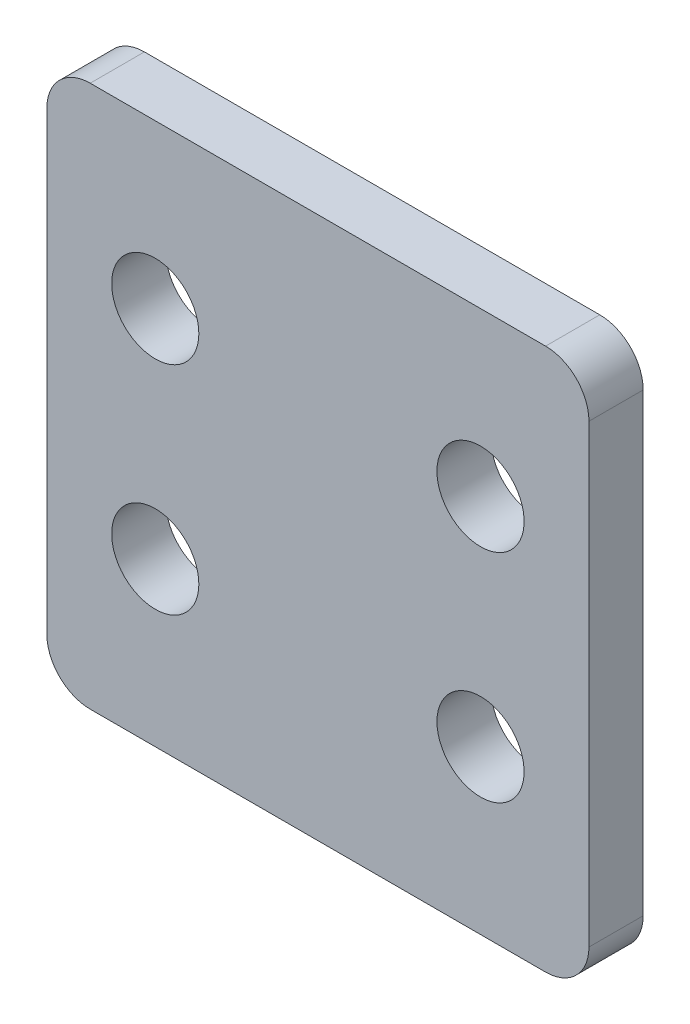
SolidWorks part; units mm, degrees
material "6061-T6 (SS)"
ref_plane "Front Plane" through (0, 0, 0) normal (0, 0, 1) x (1, 0, 0)
ref_plane "Top Plane" through (0, 0, 0) normal (0, 1, 0) x (1, 0, 0)
ref_plane "Right Plane" through (0, 0, 0) normal (1, 0, 0) x (0, 0, -1)
sketch "Sketch1" plane through (0, 0, 0) normal (0, 0, 1) x (1, 0, 0)
  line L0 (-9.525, -6.35) -> (-9.525, 6.35) construction
  line L5 (-15.875, -15.875) -> (15.875, -15.875)
  line L6 (-15.875, -15.875) -> (-15.875, 15.875)
  line L11 (-15.875, 15.875) -> (15.875, 15.875)
  line L15 (15.875, -15.875) -> (15.875, 15.875)
  line L16 (-15.875, -15.875) -> (15.875, 15.875) construction
  line L17 (-15.875, 15.875) -> (15.875, -15.875) construction
  line L18 (0, 15.875) -> (0, -15.875) construction
  circle A13 centre (-9.525, -6.35) radius 2.5527
  circle A14 centre (-9.525, 6.35) radius 2.5527
  circle A17 centre (9.525, -6.35) radius 2.5527
  circle A18 centre (9.525, 6.35) radius 2.5527
  point P0 (0, 0)
  point P13 (-9.525, 0)
  dimension "D2" = 12.7
  dimension "D4" = 19.05
  dimension "D5" = 5.1054
  dimension "D7" = 31.75
  dimension "D1" = 2
  dimension "D6" = 31.75
extrude "Boss-Extrude1" add sketch "Sketch1" along normal blind 3.175
fillet "Fillet1" radius 2.54 4 edges at (-15.875, 15.875, 1.5875) (-15.875, -15.875, 1.5875) (15.875, -15.875, 1.5875) (15.875, 15.875, 1.5875)
